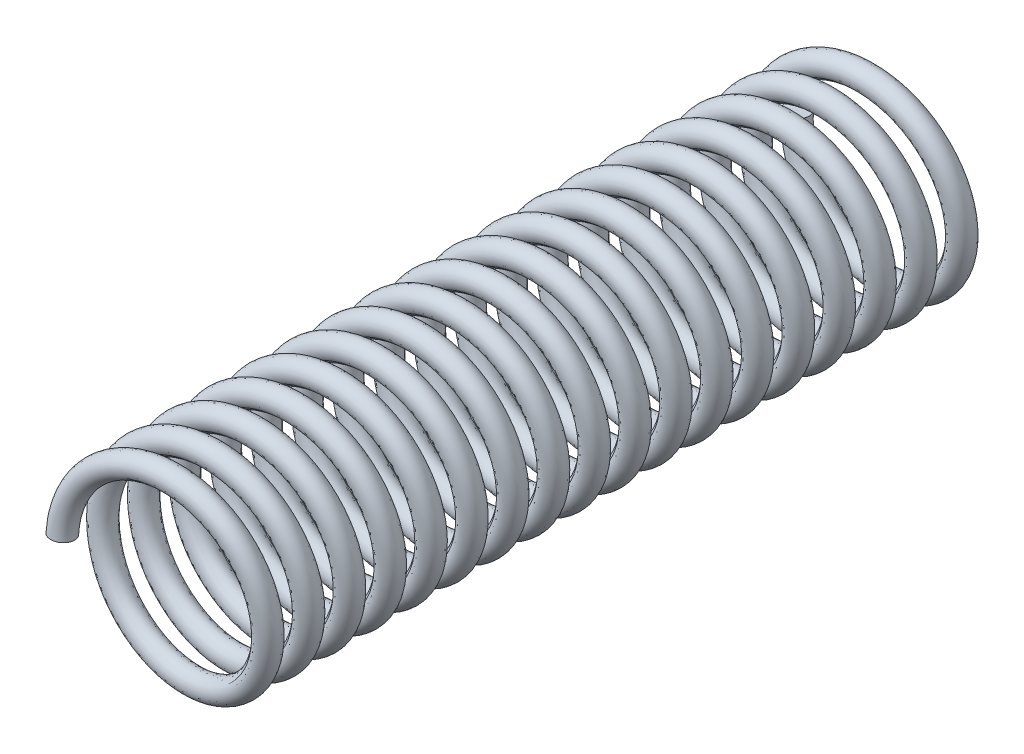
SolidWorks part; units mm, degrees
ref_plane "Front Plane" through (0, 0, 0) normal (0, 0, 1) x (1, 0, 0)
ref_plane "Top Plane" through (0, 0, 0) normal (0, 1, 0) x (1, 0, 0)
ref_plane "Right Plane" through (0, 0, 0) normal (1, 0, 0) x (0, 0, -1)
sketch "Sketch1" plane through (0, 0, 0) normal (0, 0, 1) x (1, 0, 0)
  circle A0 centre (0, 0) radius 2
  dimension "D1" = 4
curve "Helix/Spiral1" pitch 0.8833 height 15.9 turns 18
sweep "Sweep1" add path "Helix/Spiral1" circular profile diameter 0.5 parameters "D3"=0.5
sketch "Sketch8" plane through (0, 0, 0) normal (0, 0, 1) x (1, 0, 0)
  circle A0 centre (0, 0) radius 2.25 construction
  dimension "D1" = 4.5
